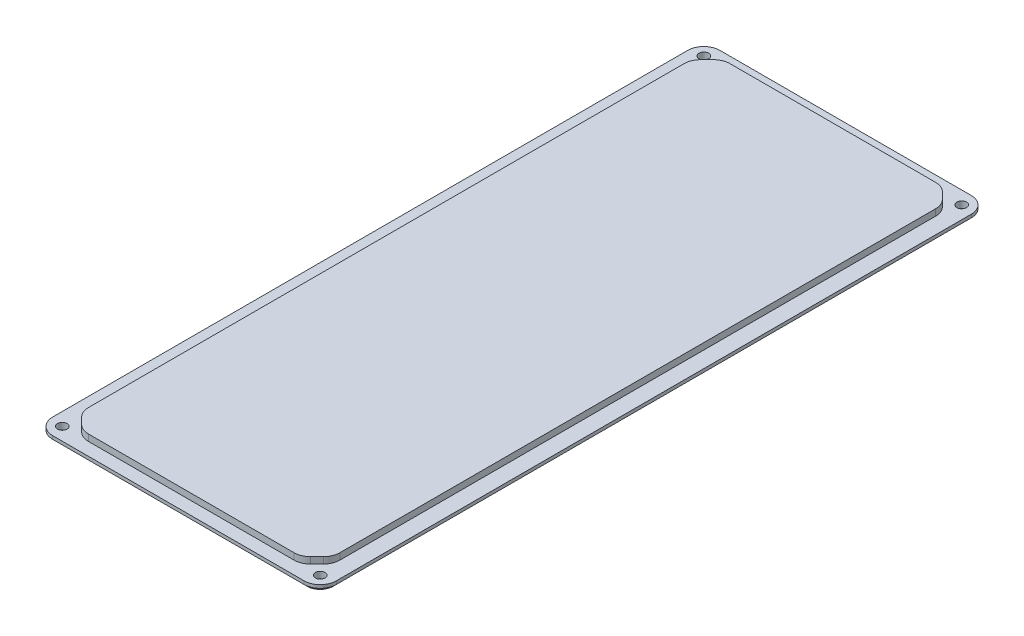
SolidWorks part; units mm, degrees
material "2014 Alloy"
ref_plane "Front Plane" through (0, 0, 0) normal (0, 0, 1) x (1, 0, 0)
ref_plane "Top Plane" through (0, 0, 0) normal (0, 1, 0) x (1, 0, 0)
ref_plane "Right Plane" through (0, 0, 0) normal (1, 0, 0) x (0, 0, -1)
sketch "Sketch1" plane through (0, 0, 0) normal (0, 1, 0) x (1, 0, 0)
  line L1 (-44, 103.5) -> (44, 103.5)
  line L2 (-44, 103.5) -> (-44, -103.5)
  line L3 (-44, -103.5) -> (44, -103.5)
  line L4 (44, 103.5) -> (44, -103.5)
  line L5 (-44, 103.5) -> (44, -103.5) construction
  line L6 (-44, -103.5) -> (44, 103.5) construction
  point P0 (0, 0)
  dimension "D1" = 88
  dimension "D2" = 207
extrude "Boss-Extrude1" add sketch "Sketch1" along normal blind 2
sketch "Sketch2" plane through (0, 2, 0) normal (0, 1, 0) x (1, 0, 0)
  line L0 (44, -103.5) -> (44, 103.5) construction
  line L1 (-39, 99.5) -> (39, 99.5)
  line L2 (-39, 99.5) -> (-39, -99.5)
  line L3 (-39, -99.5) -> (39, -99.5)
  line L4 (39, 99.5) -> (39, -99.5)
  line L5 (-39, 99.5) -> (39, -99.5) construction
  line L6 (-39, -99.5) -> (39, 99.5) construction
  point P0 (0, 0)
  dimension "D1" = 199
  dimension "D2" = 5
extrude "Boss-Extrude2" add sketch "Sketch2" along normal blind 2
chamfer "Chamfer1" distance 5 angle 45 4 edges at (-39, 3, -99.5) (39, 3, -99.5) (-39, 3, 99.5) (39, 3, 99.5)
fillet "Fillet1" radius 5 12 edges at (-44, 1, 103.5) (-39, 3, 94.5) (-34, 3, 99.5) (44, 1, 103.5) (39, 3, 94.5) (34, 3, 99.5) (44, 1, -103.5) (34, 3, -99.5) (39, 3, -94.5) (-34, 3, -99.5) (-39, 3, -94.5) (-44, 1, -103.5)
hole_wizard "Ø3.0mm Dowel Hole1" positions "Sketch4" profile "Sketch3" hole size "Ø3.0" standard "ISO"
sketch "Sketch4" plane through (0, 0, 0) normal (0, -1, 0) x (-1, 0, 0)
  line L0 (-44, -98.5) -> (-44, 98.5) construction
  line L1 (-39, 103.5) -> (39, 103.5) construction
  line L2 (44, 98.5) -> (44, -98.5) construction
  line L3 (39, -103.5) -> (-39, -103.5) construction
  point P0 (-40, 99.5)
  point P2 (40, 99.5)
  point P4 (40, -99.5)
  point P6 (-40, -99.5)
  dimension "D1" = 4
  dimension "D2" = 4
  dimension "D3" = 4
  dimension "D4" = 4
sketch "Sketch3" plane through (40, 0, -99.5) normal (1, 0, 0) x (0, 0, -1)
  line L0 (0, 0) -> (0, 18.1913)
  line L1 (0, 18.1913) -> (1.5, 17.29)
  line L2 (1.5, 17.29) -> (1.5, 0)
  line L5 (1.5, 0) -> (0, 0)
  line L10 (0, 18.1913) -> (-1.5, 17.29) construction
  line L11 (0, -6.35) -> (0, 107.95) construction
  dimension "Hole Dia." = 3
  dimension "Hole Depth" = 17.29
  dimension "Drill Angle" = 118
chamfer "Chamfer2" distance 1 angle 45 8 edges at (0, 0, 103.5) (42.5355, 0, 102.0355) (-42.5355, 0, 102.0355) (44, 0, 0) (-44, 0, 0) (42.5355, 0, -102.0355) (-42.5355, 0, -102.0355) (0, 0, -103.5)
